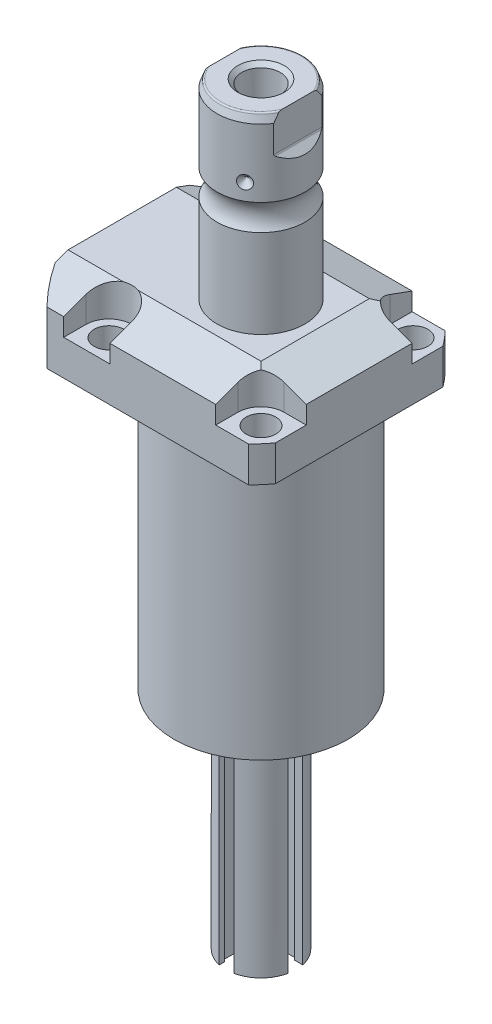
SolidWorks part; units mm, degrees
material "Alloy Steel"
ref_plane "Front Plane" through (0, 0, 0) normal (0, 0, 1) x (1, 0, 0)
ref_plane "Top Plane" through (0, 0, 0) normal (0, 1, 0) x (1, 0, 0)
ref_plane "Right Plane" through (0, 0, 0) normal (1, 0, 0) x (0, 0, -1)
sketch "Sketch1" plane through (0, 0, 0) normal (0, -1, 0) x (0, 0, 1)
  line L0 (-35.433, 50.063) -> (35.433, 50.063)
  line L1 (35.433, 50.063) -> (35.433, -35.433)
  line L2 (35.433, -35.433) -> (-35.433, -35.433)
  line L3 (-35.433, -35.433) -> (-35.433, 50.063)
  line L4 (0, 0) -> (0, -60.6467) construction
  dimension "D1" = 35.433
  dimension "D2" = 85.496
  dimension "D3" = 70.866
extrude "Extrude1" add sketch "Sketch1" against normal blind 122.047
sketch "Sketch2" plane through (0, 0, 0) normal (0, -1, 0) x (1, 0, 0)
  circle A0 centre (-5.4102, 0) radius 50.8
  dimension "D1" = 101.6
  dimension "D2" = 5.4102
extrude "Cut-Extrude1" cut sketch "Sketch2" against normal through all flip side to cut
sketch "Sketch3" plane through (0, 0, 0) normal (1, 0, 0) x (0, 0, -1)
  line L0 (31.3945, 0) -> (31.3945, 97.028)
  line L1 (31.3945, 97.028) -> (76.5937, 97.028)
  line L2 (76.5937, 97.028) -> (76.5937, 0)
  line L3 (76.5937, 0) -> (31.3945, 0)
  line L4 (0, -93.345) -> (0, 4.445) construction
  line L5 (24.2233, 0) -> (-24.2233, 0) construction
  dimension "D1" = 62.789
  dimension "D2" = 153.1874
  dimension "D3" = 97.028
revolve "Cut-Revolve1" cut sketch "Sketch3" angle 360 about L4
fillet "Fillet1" radius 0.381 1 edges at (0, 97.028, -31.3945)
sketch "Sketch4" plane through (0, 122.047, 0) normal (0, 1, 0) x (-1, 0, 0)
  line L0 (-35.433, -30.2072) -> (-35.433, 30.2072) construction
  line L1 (41.8127, 35.433) -> (-30.9923, 35.433) construction
  line L2 (-19.1008, -35.433) -> (-19.1008, -27.432)
  line L3 (-35.433, -35.433) -> (-19.1008, -35.433)
  line L4 (-35.433, -19.1008) -> (-35.433, -35.433)
  line L5 (-27.432, -19.1008) -> (-35.433, -19.1008)
  line L6 (35.7632, -35.433) -> (19.1008, -35.433)
  line L7 (19.1008, 35.433) -> (19.1008, 27.432)
  line L8 (35.7632, 35.433) -> (35.7632, 27.432)
  line L9 (35.7632, 35.433) -> (19.1008, 35.433)
  line L10 (-27.432, 19.1008) -> (-35.433, 19.1008)
  line L11 (-35.433, 19.1008) -> (-35.433, 35.433)
  line L12 (-35.433, 35.433) -> (-19.1008, 35.433)
  line L13 (-19.1008, 35.433) -> (-19.1008, 27.432)
  line L14 (-48.9217, 0) -> (49.4551, 0) construction
  line L15 (35.7632, -35.433) -> (35.7632, -27.432)
  line L16 (19.1008, -35.433) -> (19.1008, -27.432)
  arc A0 (19.1008, -27.432) -> (35.7632, -27.432) centre (27.432, -27.432) cw
  arc A1 (-27.432, -19.1008) -> (-19.1008, -27.432) centre (-27.432, -27.432) cw
  arc A2 (-27.432, 19.1008) -> (-19.1008, 27.432) centre (-27.432, 27.432) ccw
  arc A3 (19.1008, 27.432) -> (35.7632, 27.432) centre (27.432, 27.432) ccw
  dimension "D2" = 8.3312
  dimension "D1" = 27.432
  dimension "D3" = 27.432
  dimension "D4" = 54.864
extrude "Cut-Extrude2" cut sketch "Sketch4" against normal blind 12.243
sketch "Sketch5" plane through (0, 0, 0) normal (1, 0, 0) x (0, 0, -1)
  line L0 (-19.558, 122.047) -> (-35.433, 116.269)
  line L1 (0, 0) -> (0, 154.1081) construction
  line L2 (-19.558, 122.047) -> (-35.433, 122.047)
  line L3 (-35.433, 122.047) -> (-35.433, 116.269)
  dimension "D1" = 15.875
  dimension "D2" = 20
extrude "Cut-Extrude9" cut sketch "Sketch5" against normal through all and the other way through all
mirror "Mirror1" about plane through (0, 0, 0) normal (0, 0, 1) of "Cut-Extrude9"
sketch "Sketch9" plane through (0, 0, 0) normal (0, 0, 1) x (1, 0, 0)
  line L0 (19.558, 122.047) -> (35.433, 116.269)
  line L1 (35.433, 116.269) -> (35.433, 122.047)
  line L2 (35.433, 122.047) -> (19.558, 122.047)
  dimension "D1" = 15.875
  dimension "D2" = 20
extrude "Cut-Extrude7" cut sketch "Sketch9" against normal through all and the other way through all
ref_plane "Plane14" through (-35.0774, 0, 0) normal (1, 0, 0) x (0, 0, -1)
sketch "Sketch20" plane through (-35.0774, 88.9, -18.1102) normal (1, 0, 0) x (0, 1, 0)
  line L0 (-88.9, 18.1102) -> (39.8401, 18.1102) construction
  line L1 (-7.2797, 32.639) -> (36.9042, 32.639) construction
  line L2 (8.128, 38.3413) -> (9.5758, 38.3413)
  line L3 (8.128, -6.1131) -> (8.128, 42.3335) construction
  line L4 (9.5758, 38.3413) -> (9.5758, 35.8902)
  line L5 (9.5758, 35.8902) -> (10.5918, 35.8902)
  line L6 (10.5918, 35.8902) -> (10.5918, 33.8836)
  line L7 (10.5918, 33.8836) -> (21.5646, 33.8836)
  line L8 (21.5646, 33.8836) -> (21.5646, 32.639)
  line L9 (21.5646, 32.639) -> (8.128, 32.639)
  line L10 (8.128, 38.3413) -> (8.128, 32.639)
  dimension "D1" = 14.5288
  dimension "D2" = 11.4046
  dimension "D3" = 1.4478
  dimension "D4" = 6.5024
  dimension "D5" = 1.016
  dimension "D6" = 2.4892
  dimension "D7" = 10.9728
revolve "Cut-Revolve4" cut sketch "Sketch20" angle 360 about L1
mirror "Mirror10" about plane through (0, 0, 0) normal (0, 0, 1) of "Cut-Revolve4"
sketch "Sketch10" plane through (-35.0774, 88.9, -18.1102) normal (1, 0, 0) x (0, 1, 0)
  line L0 (-1.0325, 3.5814) -> (1.5659, 3.5814) construction
  line L1 (21.5646, 4.826) -> (10.5918, 4.826) construction
  line L2 (10.5918, 2.3368) -> (21.5646, 2.3368) construction
  line L4 (8.128, -12.097) -> (8.128, 48.3174) construction
  circle A0 centre (8.3947, 8.1026) radius 1.1811
  dimension "D1" = 2.3622
  dimension "D2" = 0.2667
  dimension "D3" = 9.0424
revolve "Revolve4" add sketch "Sketch10" angle 360 about L0
mirror "Mirror12" about plane through (0, 0, 0) normal (0, 0, 1) of bodies 135
sketch "Sketch15" plane through (0, 0, 0) normal (1, 0, 0) x (0, 0, -1)
  line L0 (0, 122.047) -> (15.875, 122.047)
  line L1 (15.875, 122.047) -> (15.875, 153.8901)
  line L2 (15.875, 163.3043) -> (15.875, 187.7822)
  line L3 (14.8118, 190.7032) -> (0, 190.7032)
  line L4 (0, 190.7032) -> (0, 122.047)
  line L5 (0, 250.2908) -> (0, 28.9095) construction
  line L6 (19.558, 122.047) -> (-19.558, 122.047) construction
  line L7 (14.8118, 190.7032) -> (15.875, 187.7822)
  line L9 (24.2233, 97.028) -> (35.433, 97.028) construction
  arc A0 (15.875, 163.3043) -> (15.875, 153.8901) centre (22.2504, 158.5972) ccw
  dimension "D2" = 20
  dimension "D4" = 7.9248
  dimension "D6" = 28.6512
  dimension "D1" = 93.6752
  dimension "D3" = 31.75
  dimension "D5" = 32.106
  dimension "D7" = 2.921
revolve "Revolve3" add sketch "Sketch15" angle 360 about L5
hole_wizard "Hole1" positions "Sketch18" profile "Sketch17" legacy end condition up to next
sketch "Sketch18" plane through (0, 109.804, 0) normal (0, 1, 0) x (-1, 0, 0)
  arc A0 (35.7632, -27.432) -> (19.1008, -27.432) centre (27.432, -27.432) ccw construction
  arc A1 (19.1008, 27.432) -> (35.7632, 27.432) centre (27.432, 27.432) ccw construction
  arc A2 (-27.432, 19.1008) -> (-19.1008, 27.432) centre (-27.432, 27.432) ccw construction
  arc A3 (-19.1008, -27.432) -> (-27.432, -19.1008) centre (-27.432, -27.432) ccw construction
  point P0 (-27.432, -27.432)
  point P1 (-27.432, 27.432)
  point P3 (27.432, 27.432)
  point P5 (27.432, -27.432)
sketch "Sketch17" plane through (27.432, 109.804, -27.432) normal (1, 0, 0) x (0, 0, 1)
  line L0 (0, 0) -> (0, 12.776)
  line L1 (0, 12.776) -> (5.3594, 12.776)
  line L2 (5.3594, 12.776) -> (5.3594, 0)
  line L3 (5.3594, 0) -> (0, 0)
  line L4 (0, 110) -> (0, -10) construction
  dimension "Diameter" = 10.7188
  dimension "Depth" = 12.776
chamfer "Chamfer1" distance 0.635 angle 45 2 edges at (-35.0774, 99.4918, 13.2842) (-35.0774, 99.4918, -13.2842)
ref_plane "Plane15" through (0, 109.5248, 0) normal (0, -1, 0) x (1, 0, 0)
sketch "Sketch21" plane through (0, 109.5248, 0) normal (0, -1, 0) x (1, 0, 0)
  line L0 (-57.5495, -12.9794) -> (-2.9353, -12.9794) construction
  line L1 (-50.063, -1.9304) -> (-49.809, -1.9304)
  line L2 (-49.809, -1.9304) -> (-49.809, -6.7564)
  line L3 (-49.809, -6.7564) -> (-47.2563, -7.4404)
  line L4 (-46.6957, -8.001) -> (-30.759, -8.001)
  line L5 (-30.759, -8.001) -> (-30.759, -12.9794)
  line L6 (-30.759, -12.9794) -> (-50.063, -12.9794)
  line L7 (-50.063, 24.2233) -> (-50.063, -24.2233) construction
  line L8 (-50.063, -12.9794) -> (-50.063, -1.9304)
  line L9 (-47.2563, -7.4404) -> (-46.6957, -8.001)
  dimension "D1" = 12.9794
  dimension "D2" = 0.254
  dimension "D3" = 22.098
  dimension "D4" = 45
  dimension "D5" = 2.5527
  dimension "D6" = 9.9568
  dimension "D7" = 19.05
  dimension "D8" = 15
  dimension "D9" = 12.446
revolve "Cut-Revolve5" cut sketch "Sketch21" angle 360 about L0
mirror "Mirror13" about plane through (0, 0, 0) normal (0, 0, 1) of "Cut-Revolve5"
fillet "Fillet2" radius 0.635 1 edges at (0, 190.7032, 14.8118)
sketch "Sketch26" plane through (0, 0, 0) normal (0, 0, 1) x (1, 0, 0)
  line L0 (-39.772, 169.2652) -> (35.3173, 169.2652) construction
  line L1 (-15.875, 171.6782) -> (-13.462, 169.2652)
  line L2 (-15.875, 187.7822) -> (-15.875, 163.3043) construction
  line L3 (-13.462, 169.2652) -> (-15.875, 169.2652)
  line L4 (-15.875, 169.2652) -> (-15.875, 171.6782)
  arc A0 (-15.875, 153.8901) -> (-15.875, 163.3043) centre (-22.2504, 158.5972) ccw construction
  dimension "D1" = 45
  dimension "D2" = 4.826
  dimension "D3" = 10.668
revolve "Cut-Revolve7" cut sketch "Sketch26" angle 360 about L0
pattern_circular "CirPattern1" count 3 over 360 about axis through (0, 250.2908, 0) along (0, 1, 0) of "Cut-Revolve7"
hole_wizard "Hole2" positions "Sketch28" profile "Sketch27" legacy
sketch "Sketch28" plane through (0, 190.7032, 0) normal (0, 1, 0) x (-1, 0, 0)
  circle A0 centre (0, 0) radius 15.875 construction
  point P0 (0, 0)
sketch "Sketch27" plane through (0, 190.7032, 0) normal (1, 0, 0) x (0, 0, 1)
  line L0 (0, 0) -> (0, 28.8121)
  line L1 (0, 28.8121) -> (6.9469, 24.638)
  line L2 (6.9469, 24.638) -> (6.9469, 0)
  line L4 (6.9469, 0) -> (0, 0)
  line L6 (0, 28.8121) -> (-6.9469, 24.638) construction
  line L7 (0, -4.2442) -> (0, 117.3081) construction
  dimension "Diameter" = 13.8938
  dimension "Depth" = 24.638
  dimension "Drill Angle" = 118
sketch "Sketch29" plane through (0, 0, 0) normal (0, 0, 1) x (1, 0, 0)
  line L0 (0, 0) -> (0, 192.0172) construction
  line L1 (13.284, 190.7032) -> (13.284, 178.0032)
  line L2 (14.3672, 190.7032) -> (-14.3672, 190.7032) construction
  line L3 (13.5072, 177.4644) -> (16.332, 174.6396)
  line L5 (16.332, 174.6396) -> (16.332, 190.7032)
  line L6 (16.332, 190.7032) -> (13.284, 190.7032)
  line L7 (-16.332, 190.7032) -> (-13.284, 190.7032)
  line L8 (-16.332, 174.6396) -> (-16.332, 190.7032)
  line L9 (-13.5072, 177.4644) -> (-16.332, 174.6396)
  line L10 (-13.284, 190.7032) -> (-13.284, 178.0032)
  arc A0 (13.284, 178.0032) -> (13.5072, 177.4644) centre (14.046, 178.0032) ccw
  arc A1 (-13.284, 178.0032) -> (-13.5072, 177.4644) centre (-14.046, 178.0032) cw
  dimension "D2" = 0.762
  dimension "D1" = 45
  dimension "D3" = 26.568
  dimension "D4" = 12.7
  dimension "D5" = 3.048
extrude "Cut-Extrude10" cut sketch "Sketch29" against normal through all and the other way through all
chamfer "Chamfer2" distance 1.4351 angle 45 1 edges at (0, 190.7032, 6.9469)
sketch "Sketch30" plane through (0, 0, 0) normal (0, 0, 1) x (1, 0, 0)
  line L0 (0, 75.4045) -> (0, 27.1273) construction
  line L2 (0, 0) -> (22.225, 0)
  line L3 (-31.3945, 0) -> (31.3945, 0) construction
  line L4 (22.225, 0) -> (22.225, -2.54)
  line L5 (22.225, -2.54) -> (12.7, -2.54)
  line L6 (12.7, -2.54) -> (12.7, -81.28)
  line L7 (12.7, -81.28) -> (0, -81.28)
  line L8 (0, -81.28) -> (0, 0)
  dimension "D1" = 44.45
  dimension "D2" = 25.4
  dimension "D3" = 2.54
  dimension "D4" = 81.28
revolve "Revolve5" add sketch "Sketch30" angle 360 about L0
sketch "Sketch33" plane through (0, -2.54, 0) normal (0, -1, 0) x (1, 0, 0)
  circle A0 centre (0, 0) radius 19.431 construction
  circle A2 centre (19.431, 0) radius 2.7051
  dimension "D1" = 38.862
  dimension "D2" = 5.4102
extrude "Boss-Extrude1" add sketch "Sketch33" along normal blind 2.9972
pattern_circular "CirPattern2" count 3 over 360 about axis through (0, 0, 0) along (0, 1, 0) of "Boss-Extrude1"
sketch "Sketch34" plane through (0, -81.28, 0) normal (0, -1, 0) x (1, 0, 0)
  line L2 (13.335, -2.6416) -> (9.525, -2.6416)
  line L3 (9.525, -2.6416) -> (9.525, -3.4925)
  line L4 (9.525, -3.4925) -> (6.223, -3.4925)
  line L5 (6.223, -3.4925) -> (6.223, 3.4925)
  line L6 (6.223, 3.4925) -> (10.5463, 3.4925)
  line L7 (10.5463, 3.4925) -> (10.5463, 2.6416)
  line L8 (10.5463, 2.6416) -> (13.335, 2.6416)
  line L9 (13.335, 2.6416) -> (13.335, -2.6416)
  line L10 (47.0228, 0) -> (-47.0228, 0) construction
  line L11 (0, -38.9763) -> (0, 38.9763) construction
  dimension "D1" = 6.985
  dimension "D2" = 3.4925
  dimension "D3" = 5.2832
  dimension "D4" = 2.6416
  dimension "D5" = 6.223
  dimension "D6" = 3.302
  dimension "D7" = 3.81
extrude "Cut-Extrude11" cut sketch "Sketch34" against normal blind 70.612
pattern_circular "CirPattern3" count 4 over 360 about axis through (0, 0, 0) along (0, 1, 0) of "Cut-Extrude11"
sketch "Sketch35" plane through (0, 0, 6.223) normal (0, 0, 1) x (1, 0, 0)
  line L0 (-2.6416, -10.668) -> (2.6416, -10.668) construction
  circle A0 centre (0, -10.668) radius 3.4925
  dimension "D1" = 6.985
extrude "Cut-Extrude15" cut sketch "Sketch35" along normal blind 7.62
pattern_circular "CirPattern4" count 4 over 360 about axis through (0, 75.4045, 0) along (0, 1, 0) of "Cut-Extrude15"
sketch "Sketch37" plane through (0, -5.5372, 0) normal (0, -1, 0) x (1, 0, 0)
  line L0 (19.431, 2.7051) -> (19.431, -2.7051) construction
  line L1 (16.7259, 0) -> (22.1361, 0) construction
  line L2 (19.431, 1.2446) -> (20.1473, 1.2446)
  line L3 (20.1473, 1.2446) -> (20.8659, 0)
  line L4 (20.8659, 0) -> (20.1473, -1.2446)
  line L5 (20.1473, -1.2446) -> (18.7117, -1.2446)
  line L6 (18.7117, -1.2446) -> (17.9931, 0)
  line L7 (17.9931, 0) -> (18.7117, 1.2446)
  line L8 (18.7117, 1.2446) -> (19.431, 1.2446)
  circle A0 centre (19.431, 0) radius 2.7051 construction
  circle A1 centre (19.431, 0) radius 2.7051 construction
  dimension "D1" = 30
  dimension "D2" = 30
  dimension "D3" = 30
  dimension "D4" = 30
  dimension "D5" = 2.4892
  dimension "D6" = 1.2446
  dimension "D7" = 2.8727
  dimension "D8" = 0.7163
extrude "Cut-Extrude16" cut sketch "Sketch37" against normal blind 1.27
pattern_circular "CirPattern5" count 3 over 360 about axis through (0, 0, 0) along (0, 1, 0) of "Cut-Extrude16"
sketch "Sketch39" plane through (0, -2.54, 0) normal (0, -1, 0) x (1, 0, 0)
  circle A0 centre (19.431, 0) radius 1.7272
  dimension "D1" = 3.4544
extrude "Cut-Extrude17" cut sketch "Sketch39" against normal blind 2.54
pattern_circular "CirPattern6" count 12 over 360 about axis through (0, 0, 0) along (0, 1, 0) of "Cut-Extrude17"
